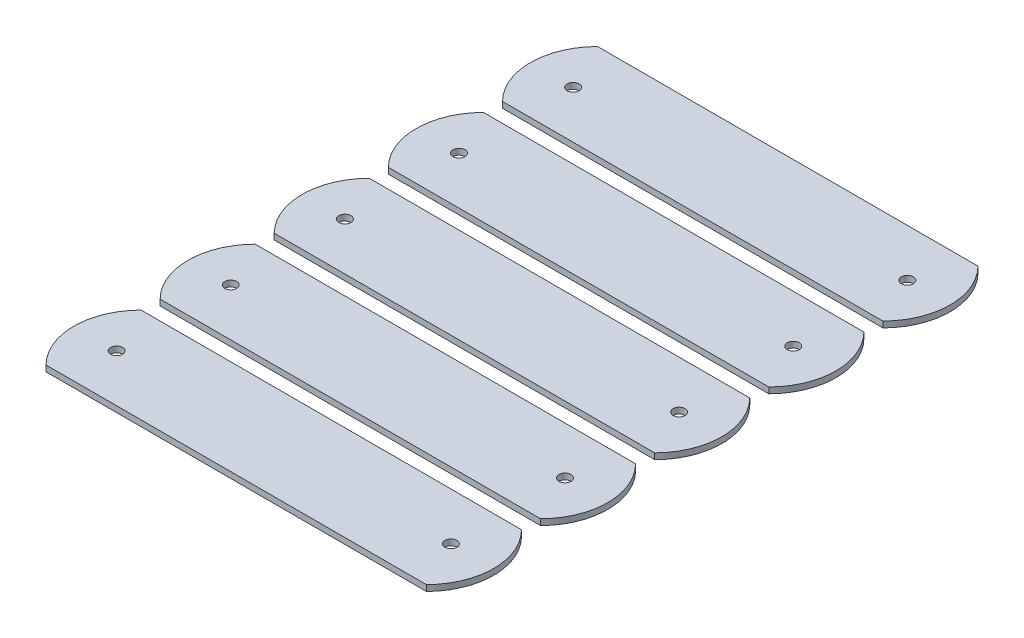
SolidWorks part; units mm, degrees
ref_plane "Front Plane" through (0, 0, 0) normal (0, 0, 1) x (1, 0, 0)
ref_plane "Top Plane" through (0, 0, 0) normal (0, 1, 0) x (1, 0, 0)
ref_plane "Right Plane" through (0, 0, 0) normal (1, 0, 0) x (0, 0, -1)
sketch "Sketch1" plane through (0, 0, 0) normal (0, 1, 0) x (1, 0, 0)
  line L0 (0, 12.7) -> (0, -12.7) construction
  line L1 (-50.8, -12.7) -> (50.8, -12.7)
  line L2 (-50.8, -12.7) -> (-50.8, 12.7)
  line L3 (-50.8, 12.7) -> (50.8, 12.7)
  line L4 (50.8, -12.7) -> (50.8, 12.7)
  line L5 (-50.8, -12.7) -> (50.8, 12.7) construction
  line L6 (-50.8, 12.7) -> (50.8, -12.7) construction
  arc A0 (-50.8, -12.7) -> (-50.8, 12.7) centre (-38.1, 0) cw
  arc A1 (50.8, 12.7) -> (50.8, -12.7) centre (38.1, 0) cw
  circle A2 centre (-44.6371, 0) radius 1.6002
  circle A3 centre (44.6371, 0) radius 1.6002
  point P0 (0, 0)
extrude "Boss-Extrude1" add sketch "Sketch1" along normal mid plane 1.5875 contours L1 L4 L3 L2 A2 A3 | A0 L2 | A1 L4
pattern_linear "LPattern1" count 5 spacing 30.48 along (0, 0, -1) of "Boss-Extrude1"
